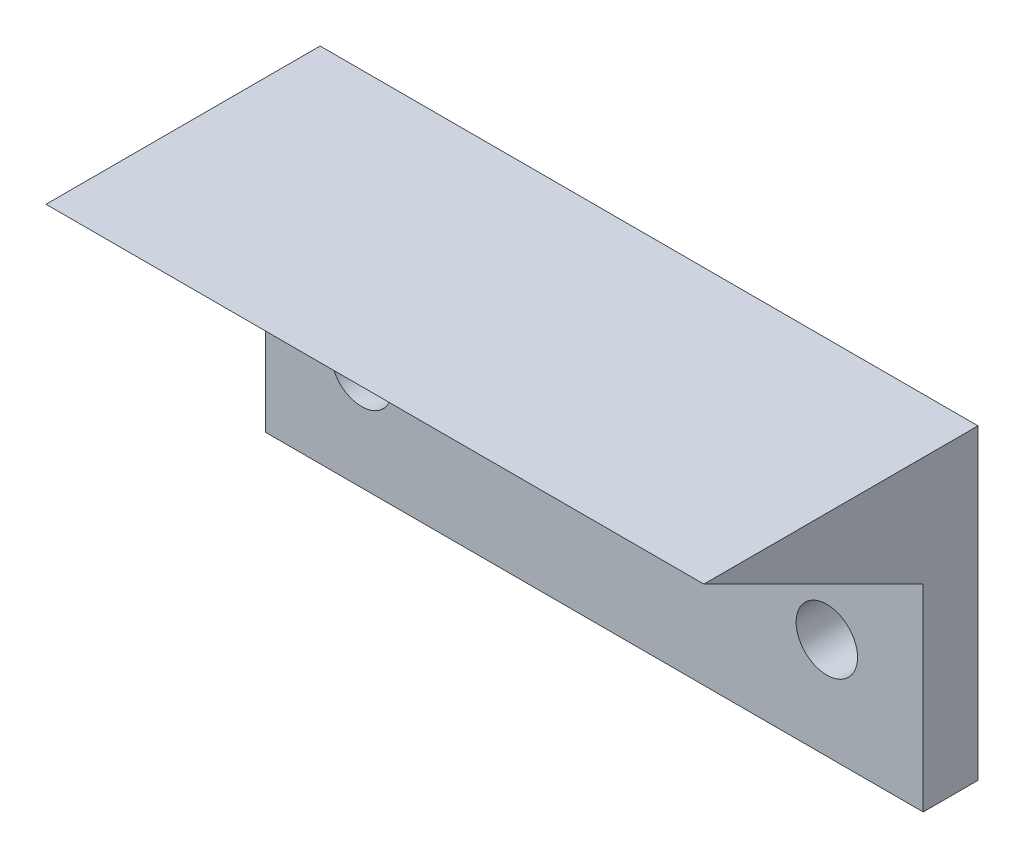
SolidWorks part; units mm, degrees
material "PET"
ref_plane "Front Plane" through (0, 0, 0) normal (0, 0, 1) x (1, 0, 0)
ref_plane "Top Plane" through (0, 0, 0) normal (0, 1, 0) x (1, 0, 0)
ref_plane "Right Plane" through (0, 0, 0) normal (1, 0, 0) x (0, 0, -1)
sketch "Sketch1" plane through (0, 0, 0) normal (0, 0, 1) x (1, 0, 0)
  line L1 (0, 0) -> (38.1, 0)
  line L2 (0, 0) -> (0, -17.78)
  line L3 (0, -17.78) -> (38.1, -17.78)
  line L4 (38.1, 0) -> (38.1, -17.78)
  circle A0 centre (5.5796, -11.9296) radius 1.778
  circle A1 centre (32.5204, -11.9296) radius 1.778
  point P9 (19.05, -17.78)
  dimension "D3" = 3.556
  dimension "D4" = 3.556
  dimension "D1" = 38.1
  dimension "D2" = 17.78
  dimension "D5" = 11.9296
  dimension "D6" = 11.9296
  dimension "D7" = 26.9408
  dimension "D8" = 13.4704
extrude "Boss-Extrude2" add sketch "Sketch1" along normal blind 3.175
sketch "Sketch4" plane through (38.1, 0, 0) normal (1, 0, 0) x (0, 0, -1)
  line L0 (-3.175, -6.35) -> (-15.875, 0)
  line L1 (-3.175, -17.78) -> (-3.175, 0) construction
  line L2 (-15.875, 0) -> (-3.175, 0)
  line L3 (-3.175, 0) -> (-3.175, -6.35)
  line L4 (-3.175, 0) -> (0, 0) construction
  dimension "D1" = 6.35
  dimension "D2" = 12.7
extrude "Boss-Extrude3" add sketch "Sketch4" against normal up to surface (38.1 mm away) up to face at (0, -8.89, 1.5875)
